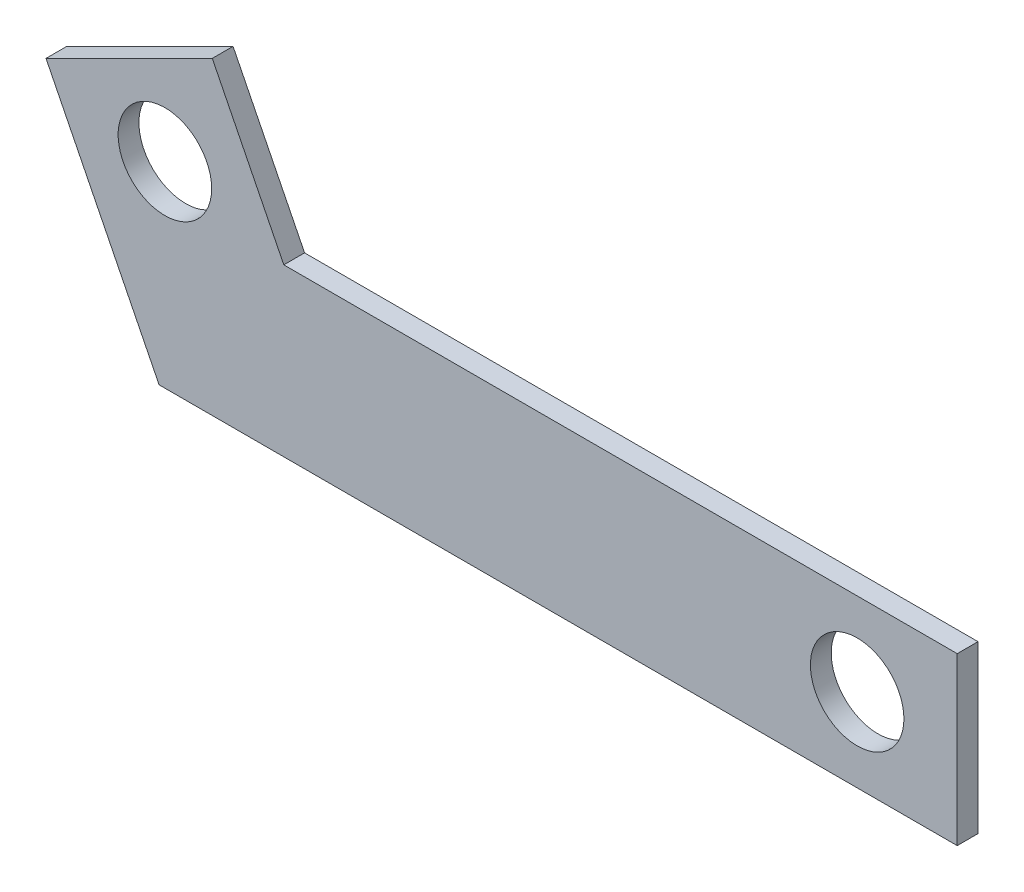
SolidWorks part; units mm, degrees
ref_plane "Front Plane" through (0, 0, 0) normal (0, 0, 1) x (1, 0, 0)
ref_plane "Top Plane" through (0, 0, 0) normal (0, 1, 0) x (1, 0, 0)
ref_plane "Right Plane" through (0, 0, 0) normal (1, 0, 0) x (0, 0, -1)
sketch "Sketch2" plane through (0, 0, 0) normal (0, 0, 1) x (1, 0, 0)
  line L0 (-139.7827, 36.9027) -> (-174.3361, 106.0095)
  line L4 (104.0573, 87.7027) -> (104.0573, 36.9027)
  line L5 (-174.3361, 106.0095) -> (-123.5361, 131.4095)
  line L6 (-123.5361, 131.4095) -> (-101.6827, 87.7027)
  line L7 (104.0573, 36.9027) -> (-139.7827, 36.9027)
  line L8 (-101.6827, 87.7027) -> (104.0573, 87.7027)
  point P0 (-212.4212, 109.5662)
  dimension "D1" = 243.84
  dimension "D2" = 50.8
  dimension "D3" = 50.8
extrude "Boss-Extrude1" add sketch "Sketch2" along normal blind 6.35
sketch "Sketch3" plane through (0, 0, 6.35) normal (0, 0, 1) x (1, 0, 0)
  circle A1 centre (73.4903, 62.3027) radius 14.2875
  circle A2 centre (-138.0094, 96.8561) radius 14.2875
  point P2 (83.1039, 62.3578)
  point P3 (80.0656, 62.3027)
  point P6 (-139.9015, 100.6401)
  point P7 (-135.3596, 96.7121)
  point P8 (78.5095, 62.3027)
  point P9 (0, 0)
  point P10 (-138.0094, 96.8561)
  point P11 (0, 0)
  point P12 (73.4903, 62.3027)
  dimension "D2" = 28.575
extrude "Cut-Extrude1" cut sketch "Sketch3" against normal blind 6.35
